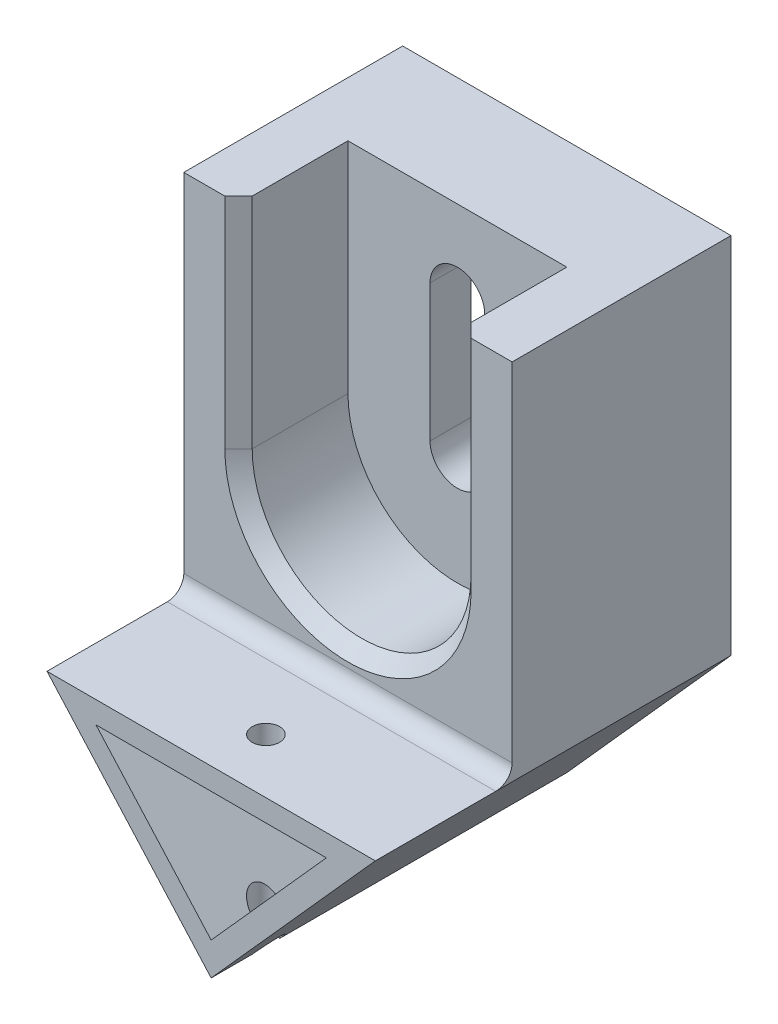
SolidWorks part; units mm, degrees
material "Copper"
ref_plane "Front Plane" through (0, 0, 0) normal (0, 0, 1) x (1, 0, 0)
ref_plane "Top Plane" through (0, 0, 0) normal (0, 1, 0) x (1, 0, 0)
ref_plane "Right Plane" through (0, 0, 0) normal (1, 0, 0) x (0, 0, -1)
sketch "Sketch1" plane through (0, 0, 0) normal (0, 0, 1) x (1, 0, 0)
  line L0 (0, 0) -> (-60, 67.082)
  line L1 (-60, 67.082) -> (60, 67.082)
  line L2 (60, 67.082) -> (0, 0)
  line L3 (0, 12) -> (-42.1115, 59.082)
  line L4 (-42.1115, 59.082) -> (42.1115, 59.082)
  line L5 (42.1115, 59.082) -> (0, 12)
  dimension "D1" = 120
  dimension "D2" = 90
  dimension "D3" = 8
extrude "Boss-Extrude1" add sketch "Sketch1" along normal blind 130
sketch "Sketch2" plane through (0, 0, 0) normal (0, 0, -1) x (-1, 0, 0)
  line L1 (-60, 67.082) -> (60, 67.082)
  line L2 (-60, 67.082) -> (-60, 200)
  line L3 (-60, 200) -> (60, 200)
  line L4 (60, 67.082) -> (60, 200)
  dimension "D1" = 200
extrude "Boss-Extrude2" add sketch "Sketch2" against normal blind 80
sketch "Sketch3" plane through (0, 67.082, 0) normal (0, 1, 0) x (1, 0, 0)
  line L0 (-60, -80) -> (60, -80) construction
  line L3 (0, -163.8614) -> (0, -23.4009) construction
  circle A0 centre (0, -110) radius 5
  dimension "D1" = 10
  dimension "D2" = 30
extrude "Cut-Extrude1" cut sketch "Sketch3" against normal through all
sketch "Sketch4" plane through (0, 0, 80) normal (0, 0, 1) x (1, 0, 0)
  line L0 (0, 294.3682) -> (0, -158.0057) construction
  line L1 (-40, 200) -> (-40, 120)
  line L2 (-60, 200) -> (60, 200) construction
  line L3 (40, 200) -> (40, 120)
  line L4 (-40, 200) -> (40, 200)
  arc A0 (-40, 120) -> (40, 120) centre (0, 120) ccw
  dimension "D1" = 40
  dimension "D2" = 80
extrude "Cut-Extrude3" cut sketch "Sketch4" against normal blind 40
chamfer "Chamfer1" distance 5 angle 45 3 edges at (40, 160, 80) (0, 80, 80) (-40, 160, 80)
fillet "Fillet1" radius 6 1 edges at (0, 67.082, 80)
sketch "Sketch5" plane through (0, 0, 40) normal (0, 0, 1) x (1, 0, 0)
  line L0 (0, 246.3711) -> (0, -57.1249) construction
  line L1 (0, 170) -> (0, 120) construction
  line L2 (10, 170) -> (10, 120)
  line L3 (-10, 170) -> (-10, 120)
  line L4 (40, 200) -> (-40, 200) construction
  arc A0 (10, 170) -> (-10, 170) centre (0, 170) ccw
  arc A1 (-10, 120) -> (10, 120) centre (0, 120) ccw
  point P5 (0, 145)
  dimension "D3" = 10
  dimension "D1" = 30
  dimension "D2" = 80
extrude "Cut-Extrude4" cut sketch "Sketch5" against normal through all
sketch "Sketch6" plane through (0, 0, 0) normal (0, 0, -1) x (-1, 0, 0)
  line L0 (60, 200) -> (-60, 200) construction
  line L1 (-42.1115, 59.082) -> (42.1115, 59.082)
  line L2 (-42.1115, 59.082) -> (-42.1115, 190)
  line L3 (-42.1115, 190) -> (42.1115, 190)
  line L4 (42.1115, 59.082) -> (42.1115, 190)
  dimension "D1" = 10
extrude "Cut-Extrude5" cut sketch "Sketch6" against normal blind 25
